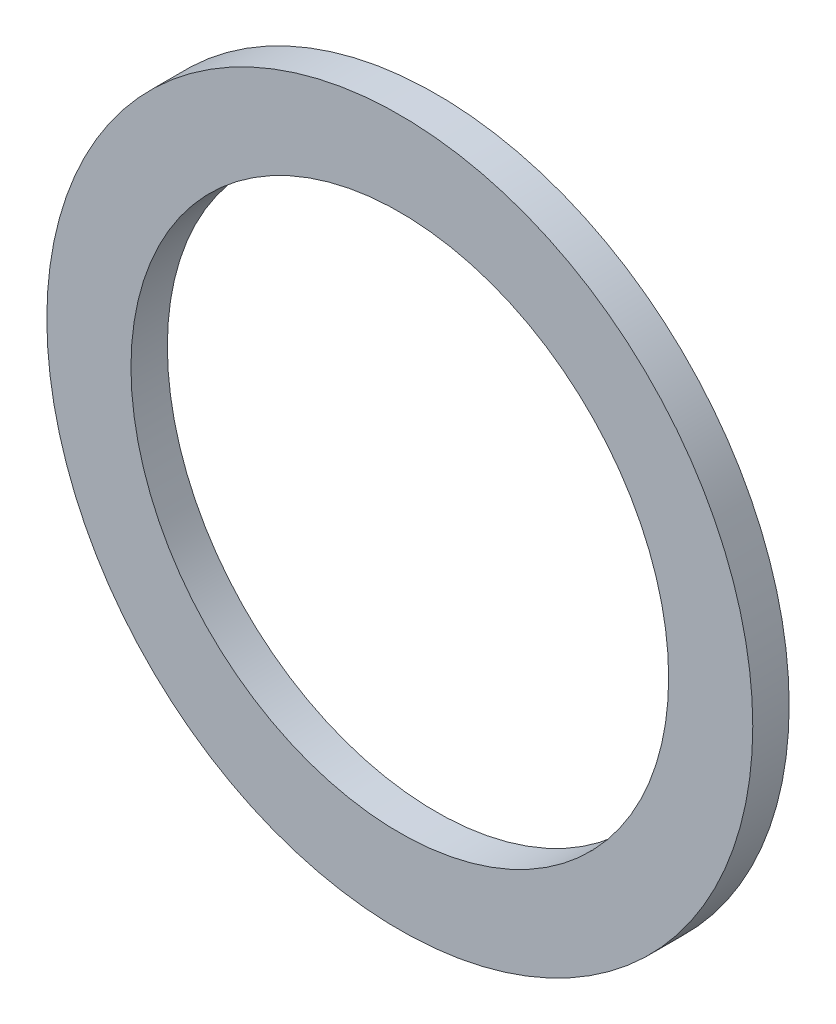
SolidWorks part; units mm, degrees
material "Alloy Steel"
ref_plane "Front Plane" through (0, 0, 0) normal (0, 0, 1) x (1, 0, 0)
ref_plane "Top Plane" through (0, 0, 0) normal (0, 1, 0) x (1, 0, 0)
ref_plane "Right Plane" through (0, 0, 0) normal (1, 0, 0) x (0, 0, -1)
sketch "Sketch1" plane through (0, 0, 0) normal (0, 0, 1) x (1, 0, 0)
  circle A0 centre (0, 0) radius 6.0071
  circle A1 centre (0, 0) radius 7.8867
  dimension "D1" = 12.0142
  dimension "D2" = 15.7734
extrude "Boss-Extrude1" add sketch "Sketch1" along normal blind 0.8128
